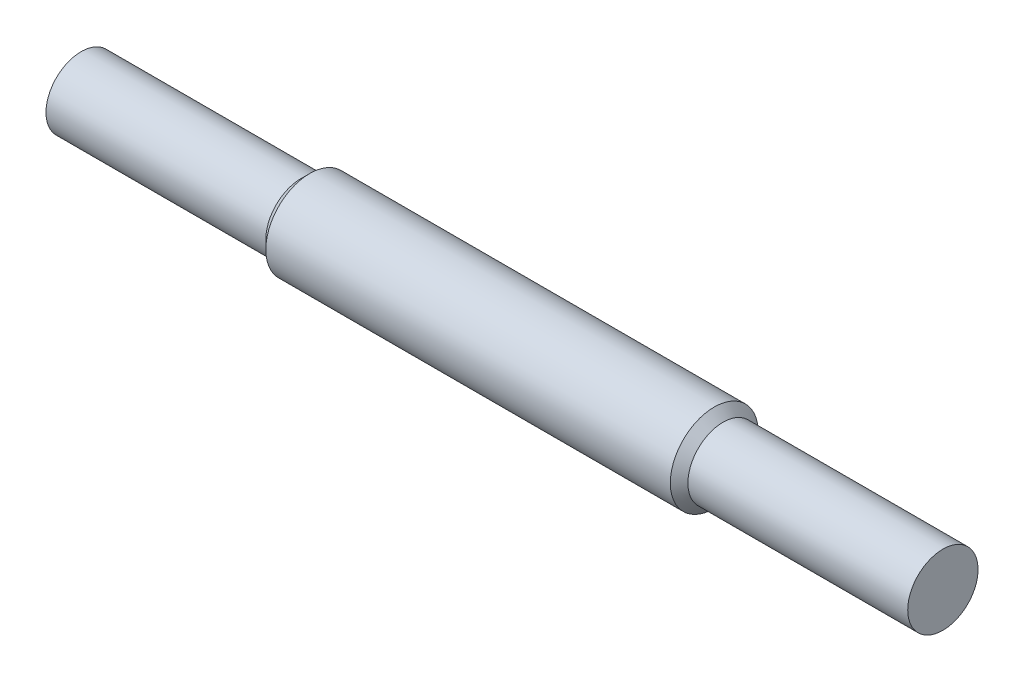
SolidWorks part; units mm, degrees
material "Stal stopowa"
ref_plane "Płaszczyzna przednia" through (0, 0, 0) normal (0, 0, 1) x (1, 0, 0)
ref_plane "Płaszczyzna górna" through (0, 0, 0) normal (0, 1, 0) x (1, 0, 0)
ref_plane "Płaszczyzna prawa" through (0, 0, 0) normal (1, 0, 0) x (0, 0, -1)
sketch "Szkic1" plane through (0, 0, 0) normal (0, 1, 0) x (1, 0, 0)
  line L0 (-25, 0) -> (23, 0)
  line L1 (-24, 5) -> (22, 5)
  line L4 (-25, 0) -> (-50, 0)
  line L5 (-25, 4) -> (-50, 4)
  line L6 (-25, 4) -> (-24, 5)
  line L7 (-50, 0) -> (-50, 4)
  line L8 (-25, 5) -> (28, 5) construction
  line L9 (-1, 0) -> (-1, 21.7082) construction
  line L10 (48, 0) -> (48, 4)
  line L11 (-25, 0) -> (28, 0) construction
  line L12 (23, 4) -> (22, 5)
  line L13 (23, 4) -> (48, 4)
  line L14 (23, 0) -> (48, 0)
  point P4 (0, 0)
  point P13 (-1, 5)
  dimension "D1" = 25
  dimension "D3" = 4
  dimension "D4" = 135
  dimension "D5" = 25
  dimension "D6" = 135
  dimension "D7" = 4
  dimension "D9" = 25
  dimension "D2" = 5
revolve "Obrót1" add sketch "Szkic1" angle 360 about L0
